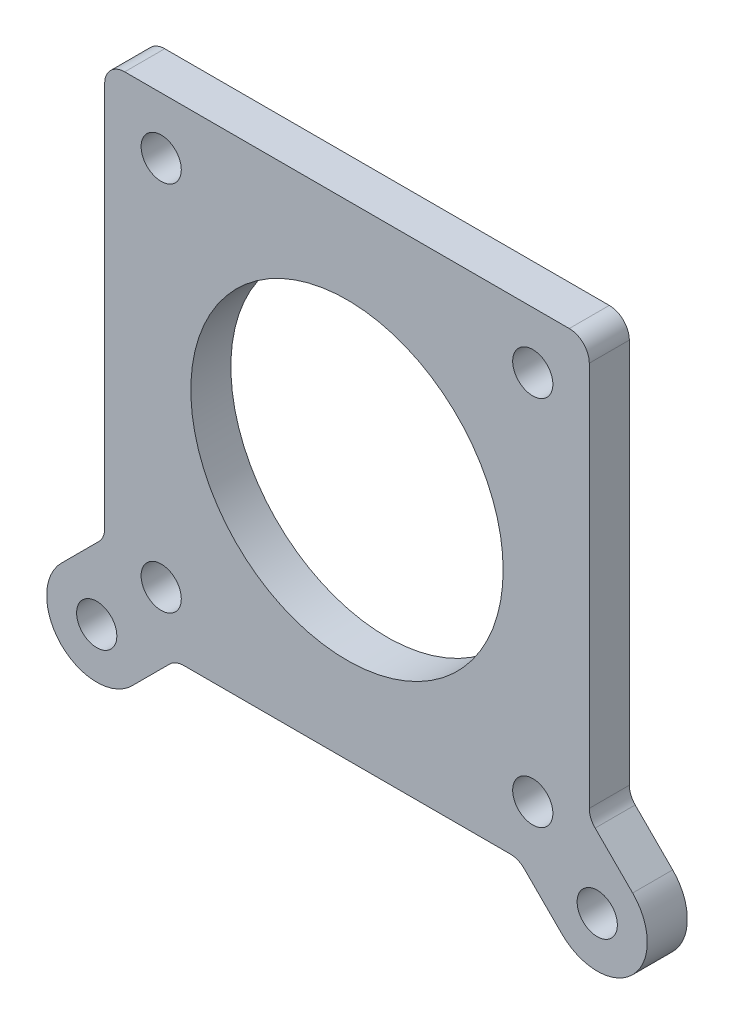
SolidWorks part; units mm, degrees
ref_plane "Front Plane" through (0, 0, 0) normal (0, 0, 1) x (1, 0, 0)
ref_plane "Top Plane" through (0, 0, 0) normal (0, 1, 0) x (1, 0, 0)
ref_plane "Right Plane" through (0, 0, 0) normal (1, 0, 0) x (0, 0, -1)
sketch "Sketch1" plane through (0, 0, 0) normal (0, 0, 1) x (1, 0, 0)
  line L0 (23.755, 28.2) -> (-23.755, 28.2) construction
  line L1 (-30.74, 30.74) -> (30.74, 30.74)
  line L2 (-30.74, 30.74) -> (-30.74, -30.74)
  line L3 (-30.74, -30.74) -> (30.74, -30.74)
  line L4 (30.74, 30.74) -> (30.74, -30.74)
  line L5 (-28.2, 23.755) -> (-28.2, -23.755) construction
  line L6 (28.2, -23.755) -> (28.2, 23.755) construction
  line L8 (-23.755, -28.2) -> (23.755, -28.2) construction
  circle A0 centre (-23.57, 23.57) radius 2.55
  circle A1 centre (23.57, 23.57) radius 2.55
  circle A2 centre (23.57, -23.57) radius 2.55
  circle A3 centre (-23.57, -23.57) radius 2.55
  circle A6 centre (0, 0) radius 19.812
  circle A7 centre (0, 0) radius 19.812
  dimension "D2" = 2.54
  dimension "D3" = 2.54
  dimension "D1" = 2.54
  dimension "D4" = 2.54
  dimension "D5" = 0.762
extrude "Boss-Extrude1" add sketch "Sketch1" against normal blind 5.08
fillet "Fillet1" radius 2.54 4 edges at (30.74, -30.74, -2.54) (-30.74, -30.74, -2.54) (-30.74, 30.74, -2.54) (30.74, 30.74, -2.54)
sketch "Sketch7" plane through (0, 0, 0) normal (0, 0, 1) x (1, 0, 0)
  line L0 (0, 0) -> (-28.2, -28.2) construction
  line L1 (-27.2599, -36.2401) -> (-21.7597, -30.74)
  line L2 (-36.2401, -27.2599) -> (-27.2599, -36.2401) construction
  line L3 (-36.2401, -27.2599) -> (-30.74, -21.7597)
  line L4 (-30.74, 28.2) -> (-30.74, -28.2) construction
  line L5 (-30.74, -21.7597) -> (-21.7597, -30.74)
  line L6 (0, -30.74) -> (0, 0) construction
  line L7 (-28.2, -30.74) -> (28.2, -30.74) construction
  line L8 (30.74, -21.7597) -> (21.7597, -30.74)
  line L9 (36.2401, -27.2599) -> (30.74, -21.7597)
  line L10 (27.2599, -36.2401) -> (21.7597, -30.74)
  arc A0 (-36.2401, -27.2599) -> (-27.2599, -36.2401) centre (-31.75, -31.75) ccw
  arc A4 (36.2401, -27.2599) -> (27.2599, -36.2401) centre (31.75, -31.75) cw
  dimension "D1" = 12.7
  dimension "D2" = 31.75
extrude "Boss-Extrude2" add sketch "Sketch7" against normal through all
fillet "Fillet2" radius 2.54 4 edges at (30.74, -21.7597, -2.54) (21.7597, -30.74, -2.54) (-21.7597, -30.74, -2.54) (-30.74, -21.7597, -2.54)
hole_wizard "#10 Clearance Hole1" positions "Sketch3" profile "Sketch2" hole size "#10" standard "ANSI Inch" end condition through all
sketch "Sketch3" plane through (0, 0, 0) normal (0, 0, 1) x (1, 0, 0)
  line L0 (-36.2401, -36.2401) -> (0, 0) construction
  line L1 (0, 0) -> (0, -30.74) construction
  line L4 (36.2401, -36.2401) -> (0, 0) construction
  line L5 (-20.7076, -30.74) -> (20.7076, -30.74) construction
  arc A3 (-36.2401, -27.2599) -> (-27.2599, -36.2401) centre (-31.75, -31.75) ccw construction
  point P9 (-31.75, -31.75)
  point P23 (31.75, -31.75)
sketch "Sketch2" plane through (-31.75, -31.75, 0) normal (1, 0, 0) x (0, -1, 0)
  line L0 (0, 0) -> (0, 5.08)
  line L1 (0, 5.08) -> (2.5527, 5.08)
  line L2 (2.5527, 5.08) -> (2.5527, 0)
  line L5 (2.5527, 0) -> (0, 0)
  line L11 (0, -6.35) -> (0, 107.95) construction
  dimension "Thru Hole Dia." = 5.1054
  dimension "Thru Hole Depth" = 5.08
